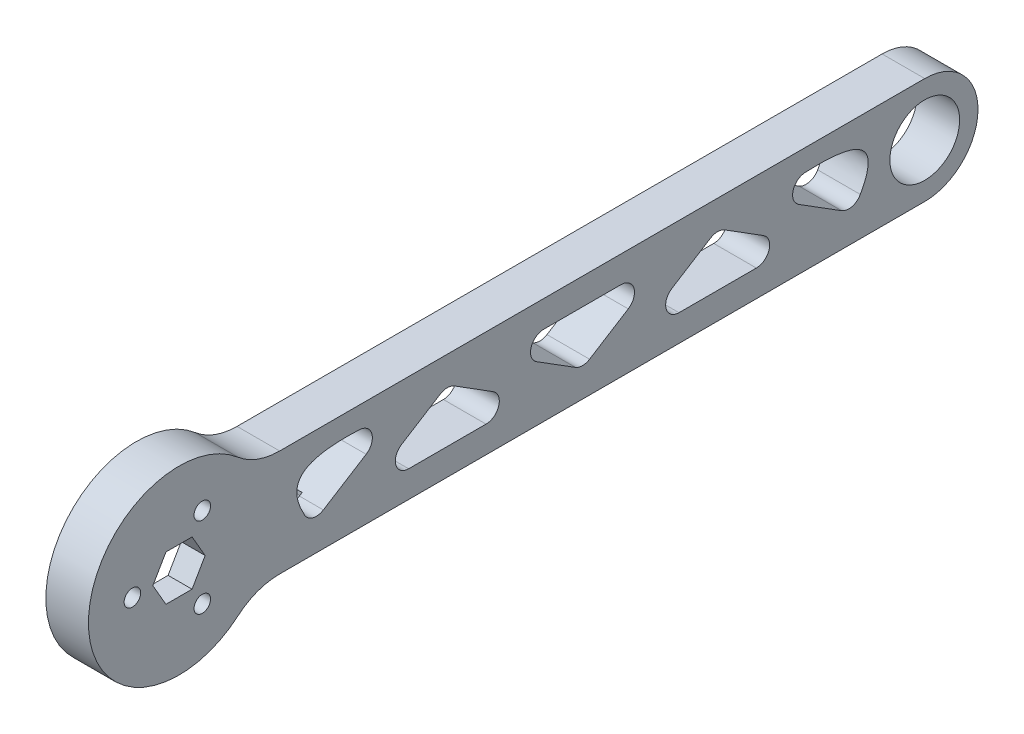
SolidWorks part; units mm, degrees
material "Thornel Mat VMA"
ref_plane "前视基准面" through (0, 0, 0) normal (0, 0, 1) x (1, 0, 0)
ref_plane "上视基准面" through (0, 0, 0) normal (0, 1, 0) x (1, 0, 0)
ref_plane "右视基准面" through (0, 0, 0) normal (1, 0, 0) x (0, 0, -1)
ref_plane "基准面4" through (-4, 0, 0) normal (-1, 0, 0) x (0, -1, 0)
sketch "草图1" plane through (-4, 0, 0) normal (-1, 0, 0) x (0, -1, 0)
  line L0 (-4.1682, -99.7975) -> (0.3816, -92.5368)
  line L1 (5, -93.8643) -> (5, -108.3857)
  line L2 (0.3816, -109.7132) -> (-4.1682, -102.4525)
  line L3 (-1.3479, -116.3696) -> (3.6833, -124.3987)
  line L4 (0.3816, -58.9632) -> (-4.1682, -51.7025)
  line L5 (-4.1682, -49.0475) -> (0.3816, -41.7868)
  line L6 (5, -43.1143) -> (5, -57.6357)
  line L7 (3.6833, -27.1013) -> (-1.3479, -35.1304)
  line L8 (4.1682, -77.0775) -> (-0.3816, -84.3382)
  line L9 (-5, -83.0107) -> (-5, -68.4893)
  line L10 (-0.3816, -67.1618) -> (4.1682, -74.4225)
  line L11 (-10, -18.8944) -> (-10, -140)
  line L12 (10, -140) -> (10, -18.8944)
  arc A0 (-4.1682, -102.4525) -> (-4.1682, -99.7975) centre (-2.0497, -101.125) cw
  arc A1 (0.3816, -92.5368) -> (5, -93.8643) centre (2.5, -93.8643) cw
  arc A2 (5, -108.3857) -> (0.3816, -109.7132) centre (2.5, -108.3857) cw
  arc A3 (-5.9631, -117.5695) -> (-1.3479, -116.3696) centre (-3.4664, -117.6971) cw
  arc A4 (3.6833, -124.3987) -> (2.7929, -127.9037) centre (1.5648, -125.7262) cw
  arc A5 (5, -57.6357) -> (0.3816, -58.9632) centre (2.5, -57.6357) cw
  arc A6 (-4.1682, -51.7025) -> (-4.1682, -49.0475) centre (-2.0497, -50.375) cw
  arc A7 (0.3816, -41.7868) -> (5, -43.1143) centre (2.5, -43.1143) cw
  arc A8 (-1.3479, -35.1304) -> (-5.9631, -33.9305) centre (-3.4664, -33.8029) cw
  arc A9 (2.7929, -23.5963) -> (3.6833, -27.1013) centre (1.5648, -25.7738) cw
  arc A10 (4.1682, -74.4225) -> (4.1682, -77.0775) centre (2.0497, -75.75) cw
  arc A11 (-0.3816, -84.3382) -> (-5, -83.0107) centre (-2.5, -83.0107) cw
  arc A12 (-5, -68.4893) -> (-0.3816, -67.1618) centre (-2.5, -68.4893) cw
  circle A13 centre (0, -140) radius 6.55
  arc A14 (10, -18.8944) -> (12.8966, -11.0761) centre (22, -18.8944) cw
  arc A15 (12.8966, -11.0761) -> (-12.8966, -11.0761) centre (0, 0) ccw
  arc A16 (-12.8966, -11.0761) -> (-10, -18.8944) centre (-22, -18.8944) cw
  arc A17 (-10, -140) -> (10, -140) centre (0, -140) ccw
  spline S0 degree 3 poles (2.7929, -127.9037) (-2.8776, -131.1016) (-5.9854, -127.8082) (-6.0768, -119.7933) (-5.9631, -117.5695) knots 0.005409 0.005409 0.005409 0.005409 0.69354 0.980498 0.980498 0.980498 0.980498
  spline S1 degree 3 poles (-5.9631, -33.9305) (-6.0768, -31.7067) (-5.9854, -23.6918) (-2.8776, -20.3984) (2.7929, -23.5963) knots 0.005409 0.005409 0.005409 0.005409 0.292367 0.980498 0.980498 0.980498 0.980498
extrude "凸台-拉伸1" add sketch "草图1" against normal blind 8
sketch "草图2" plane through (-4, 0, 0) normal (-1, 0, 0) x (0, 0, 1)
  line L0 (-23.7946, 5) -> (-27.6254, 5)
  line L1 (-23.7946, 5) -> (-10.5076, 5)
  line L3 (-23.7946, -5) -> (-10.5076, -5)
  line L5 (-23.7946, 5) -> (-11.1, 0) construction
  line L6 (-23.7946, -5) -> (-11.1, 0) construction
  line L7 (-27.6254, 5) -> (-27.6254, -4.0396)
  line L8 (-23.7946, -5) -> (-26.665, -5)
  arc A0 (-9.6392, -5.5041) -> (-9.6392, 5.5041) centre (0, 0) ccw
  arc A1 (-10.5076, 5) -> (-9.6392, 5.5041) centre (-10.5076, 6) ccw
  arc A2 (-10.5076, -5) -> (-9.6392, -5.5041) centre (-10.5076, -6) cw
  arc A3 (-27.6254, -4.0396) -> (-26.665, -5) centre (-26.665, -4.0396) ccw
  point P3 (-11.1, 0)
  dimension "D1" = 1
  dimension "D2" = 0.9604
extrude "切除-拉伸1" cut sketch "草图2" against normal blind 3.5
sketch "草图3" plane through (-0.5, 0, 0) normal (-1, 0, 0) x (0, 0, 1)
  line L0 (-4.375, 7.5777) -> (0, 0) construction
  line L1 (0, 0) -> (8.75, 0) construction
  line L2 (0, 0) -> (-4.375, -7.5777) construction
  line L3 (-31.405, 0) -> (31.405, 0) construction
  line L5 (4.9075, 0) -> (2.4537, 4.25)
  line L6 (2.4537, 4.25) -> (-2.4537, 4.25)
  line L7 (-2.4537, 4.25) -> (-4.9075, 0)
  line L8 (-4.9075, 0) -> (-2.4537, -4.25)
  line L9 (-2.4537, -4.25) -> (2.4537, -4.25)
  line L10 (2.4537, -4.25) -> (4.9075, 0)
  circle A0 centre (0, 0) radius 8.75 construction
  circle A1 centre (-4.375, 7.5777) radius 1.55
  circle A2 centre (-4.375, -7.5777) radius 1.55
  circle A3 centre (8.75, 0) radius 1.55
  circle A4 centre (0, 0) radius 4.25 construction
  point P12 (0, 0)
  dimension "D1" = 60
  dimension "D2" = 60
extrude "切除-拉伸2" cut sketch "草图3" against normal through all
